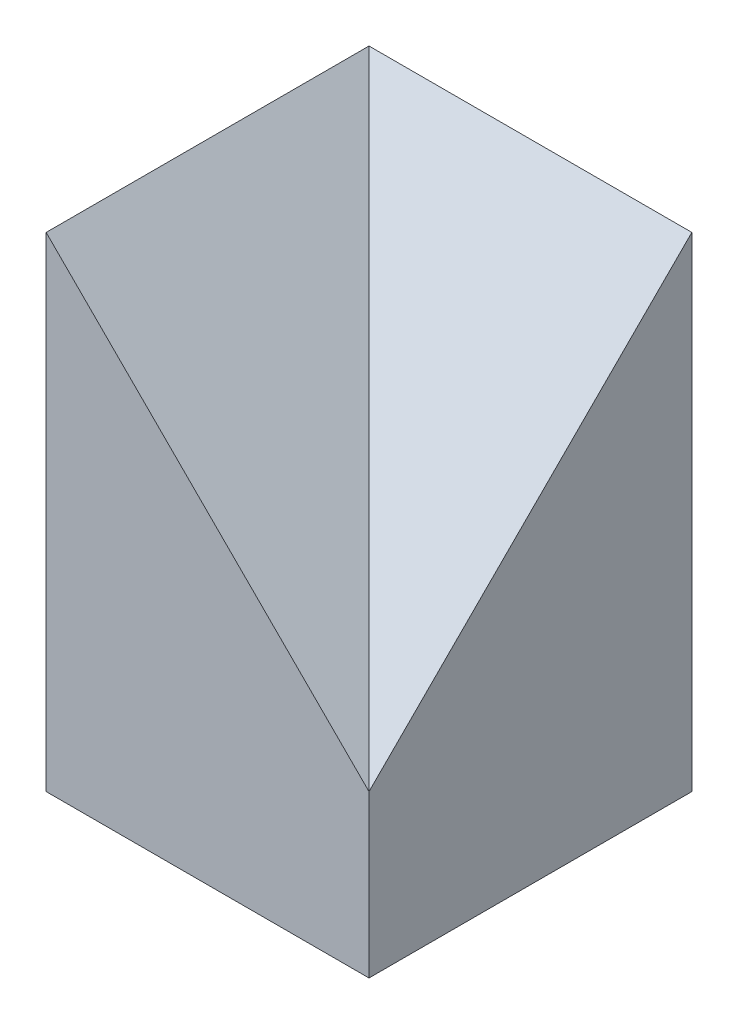
SolidWorks part; units mm, degrees
ref_plane "Ebene vorne" through (0, 0, 0) normal (0, 0, 1) x (1, 0, 0)
ref_plane "Ebene oben" through (0, 0, 0) normal (0, 1, 0) x (1, 0, 0)
ref_plane "Ebene rechts" through (0, 0, 0) normal (1, 0, 0) x (0, 0, -1)
sketch "Skizze1" plane through (0, 0, 0) normal (0, 1, 0) x (1, 0, 0)
  line L1 (0, 0) -> (400, 0)
  line L2 (0, 0) -> (0, -400)
  line L3 (0, -400) -> (400, -400)
  line L4 (400, 0) -> (400, -400)
  dimension "D1" = 400
extrude "Aufsatz-Linear austragen1" add sketch "Skizze1" along normal blind 200
sketch "Skizze2" plane through (0, 200, 0) normal (0, 1, 0) x (1, 0, 0)
  line L1 (0, 0) -> (400, 0)
  line L2 (0, 0) -> (0, -400)
  line L3 (0, -400) -> (400, -400)
  line L4 (400, 0) -> (400, -400)
ref_plane "Ebene1" through (0, 600, 0) normal (0, 1, 0) x (1, 0, 0)
sketch "Skizze3" plane through (0, 600, 0) normal (0, 1, 0) x (1, 0, 0)
  line L0 (0, -400) -> (400, -400) construction
  line L1 (400, 0) -> (400, -400) construction
  line L2 (0, 0) -> (400, 0) construction
  line L3 (0, 0) -> (0, -400) construction
  line L4 (0, -400) -> (400, -400)
  line L5 (400, 0) -> (400, -400)
  line L6 (0, 0) -> (400, 0)
  line L7 (0, 0) -> (0, -400)
  point P4 (0, 0)
sketch3d "3D-Skizze2"
  line L1 (400, 200, 400) -> (0, 200, 400)
  line L2 (0, 200, 0) -> (0, 200, 400)
  line L3 (400, 200, 0) -> (0, 200, 0)
  line L4 (0, 600, 0) -> (0, 200, 0)
  line L7 (400, 200, 400) -> (400, 200, 0)
  line L8 (400, 600, 0) -> (400, 200, 0)
  line L9 (400, 200, 400) -> (400, 600, 0)
  line L10 (400, 200, 400) -> (0, 600, 400)
  line L11 (0, 600, 400) -> (0, 200, 400)
  line L12 (0, 600, 400) -> (0, 600, 0)
  line L13 (400, 600, 0) -> (0, 600, 0)
  line L14 (400, 200, 400) -> (0, 600, 0)
extrude "Aufsatz-Linear austragen2" add sketch "Skizze2" along normal up to vertex (400 mm away) up to point (0, 600, 0)
extrude "Schnitt-Linear austragen1" cut sketch "Skizze3" along direction (-0.5774, 0.5774, -0.5774) on the side against the normal through all
